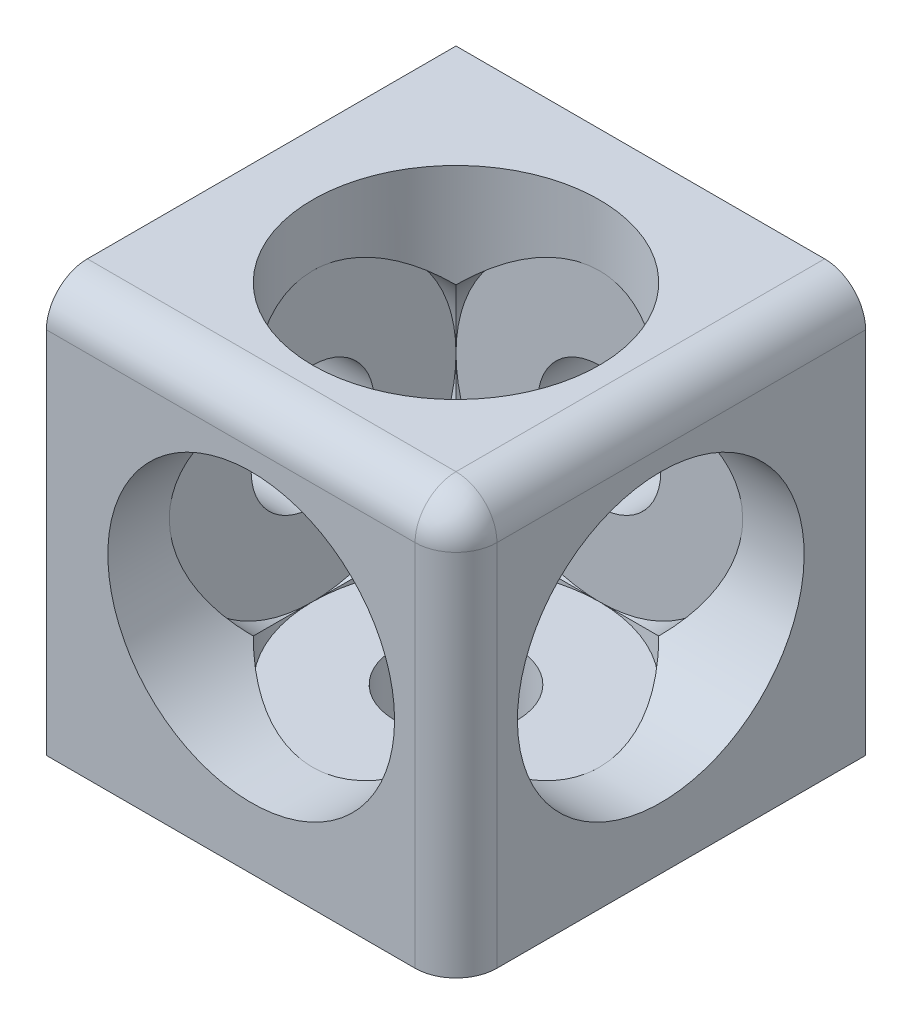
SolidWorks part; units mm, degrees
ref_plane "Plan de face" through (0, 0, 0) normal (0, 0, 1) x (1, 0, 0)
ref_plane "Plan de dessus" through (0, 0, 0) normal (0, 1, 0) x (1, 0, 0)
ref_plane "Plan de droite" through (0, 0, 0) normal (1, 0, 0) x (0, 0, -1)
sketch "Esquisse1" plane through (0, 0, 0) normal (0, 0, 1) x (1, 0, 0)
  line L1 (-20, 20) -> (0, 20)
  line L2 (-20, 20) -> (-20, 0)
  line L3 (-20, 0) -> (0, 0)
  line L4 (0, 20) -> (0, 0)
  dimension "D1" = 20
  dimension "D2" = 20
extrude "Boss.-Extru.1" add sketch "Esquisse1" along normal blind 20
fillet "Congé1" radius 2 3 edges at (0, 10, 20) (-10, 20, 20) (0, 20, 10)
sketch "Esquisse2" plane through (0, 0, 20) normal (0, 0, 1) x (1, 0, 0)
  line L0 (-20, 0) -> (-2, 0) construction
  line L1 (-20, 18) -> (-20, 0) construction
  circle A0 centre (-10, 10) radius 3
  dimension "D1" = 6
  dimension "D2" = 10
  dimension "D3" = 10
extrude "Enlèv. mat.-Extru.1" cut sketch "Esquisse2" against normal through all
sketch "Esquisse3" plane through (0, 0, 0) normal (1, 0, 0) x (0, 0, -1)
  line L0 (-18, 0) -> (0, 0) construction
  line L1 (0, 0) -> (0, 18) construction
  circle A0 centre (-10, 10) radius 3
  dimension "D1" = 6
  dimension "D2" = 10
  dimension "D3" = 10
extrude "Enlèv. mat.-Extru.2" cut sketch "Esquisse3" against normal through all
sketch "Esquisse4" plane through (0, 20, 0) normal (0, 1, 0) x (-1, 0, 0)
  line L0 (2, 0) -> (20, 0) construction
  line L1 (20, 18) -> (20, 0) construction
  circle A0 centre (10, 10) radius 3
  dimension "D1" = 6
  dimension "D2" = 10
  dimension "D3" = 10
extrude "Enlèv. mat.-Extru.3" cut sketch "Esquisse4" against normal through all
sketch "Esquisse5" plane through (0, 0, 20) normal (0, 0, 1) x (1, 0, 0)
  circle A0 centre (-10, 10) radius 7
  dimension "D1" = 14
extrude "Enlèv. mat.-Extru.4" cut sketch "Esquisse5" against normal blind 17
sketch "Esquisse6" plane through (0, 0, 0) normal (1, 0, 0) x (0, 0, -1)
  circle A0 centre (-10, 10) radius 7
  dimension "D1" = 14
extrude "Enlèv. mat.-Extru.5" cut sketch "Esquisse6" against normal blind 17
sketch "Esquisse7" plane through (0, 20, 0) normal (0, 1, 0) x (1, 0, 0)
  circle A0 centre (-10, -10) radius 7
  dimension "D1" = 14
extrude "Enlèv. mat.-Extru.6" cut sketch "Esquisse7" against normal blind 17
